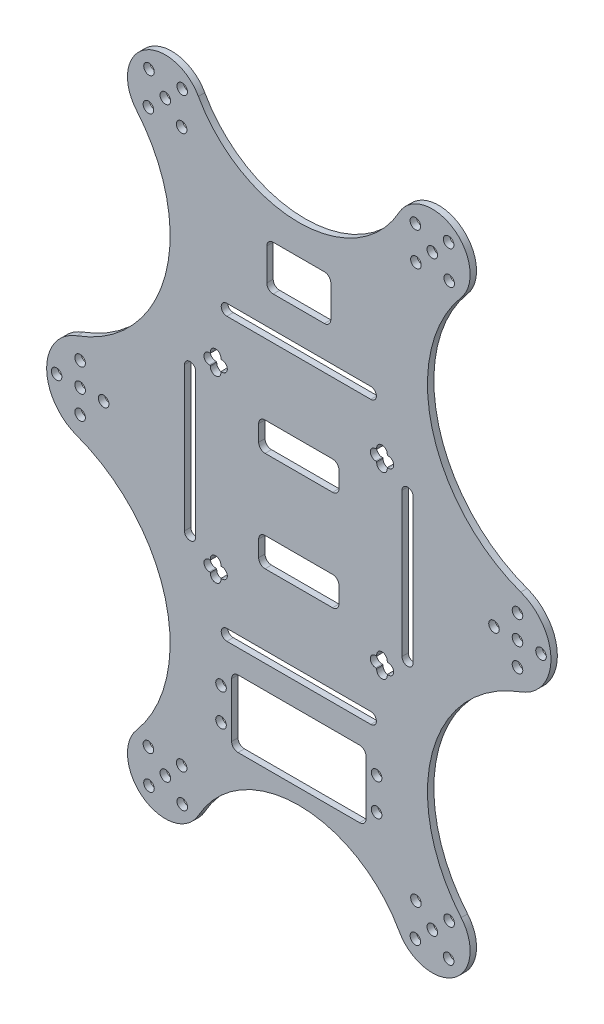
SolidWorks part; units mm, degrees
ref_plane "前视基准面" through (0, 0, 0) normal (0, 0, 1) x (1, 0, 0)
ref_plane "上视基准面" through (0, 0, 0) normal (0, 1, 0) x (1, 0, 0)
ref_plane "右视基准面" through (0, 0, 0) normal (1, 0, 0) x (0, 0, -1)
sketch "草图1" plane through (0, 0, 0) normal (0, 0, 1) x (1, 0, 0)
  line L0 (4.4926, -1.2596) -> (4.4926, -27.7633) construction
  line L1 (109.289, 84.436) -> (119.8633, 74.2245) construction
  line L2 (-7.014, -12.3723) -> (212.2703, -12.3723) construction
  line L3 (26.0221, 84.6174) -> (36.2336, 74.0431) construction
  line L4 (36.415, 84.436) -> (25.8407, 74.2245) construction
  line L5 (72.852, 157.0661) -> (72.852, -150.5607) construction
  line L6 (119.6818, 84.6174) -> (109.4704, 74.0431) construction
  line L7 (141.2114, -1.2596) -> (141.2114, -27.7633) construction
  line L8 (119.6818, -109.362) -> (109.4704, -98.7877) construction
  line L9 (36.415, -109.1806) -> (25.8407, -98.9691) construction
  line L10 (26.0221, -109.362) -> (36.2336, -98.7877) construction
  line L11 (109.289, -109.1806) -> (119.8633, -98.9691) construction
  line L12 (95.352, 33.3777) -> (50.352, 33.3777)
  line L13 (38.852, 21.4961) -> (38.852, -51.8522) construction
  line L14 (40.602, 10.1277) -> (40.602, -34.8723)
  line L15 (37.102, -34.8723) -> (37.102, 10.1277)
  line L16 (108.602, -34.8723) -> (108.602, 10.1277)
  line L17 (105.102, 10.1277) -> (105.102, -34.8723)
  line L18 (95.352, -58.1223) -> (50.352, -58.1223)
  line L19 (50.352, 29.8777) -> (95.352, 29.8777)
  line L20 (50.352, -54.6223) -> (95.352, -54.6223)
  line L21 (106.165, 15.6277) -> (41.102, 15.6277) construction
  line L22 (92.7157, 50.1512) -> (51.4618, 50.1512) construction
  line L23 (98.852, 21.4961) -> (98.852, -45.901) construction
  line L24 (80.852, 57.1512) -> (64.852, 57.1512)
  line L25 (82.852, 55.1512) -> (82.852, 45.1512)
  line L26 (80.852, 43.1512) -> (64.852, 43.1512)
  line L27 (62.852, 55.1512) -> (62.852, 45.1512)
  line L28 (82.852, 57.1512) -> (62.852, 43.1512) construction
  line L29 (82.852, 43.1512) -> (62.852, 57.1512) construction
  line L30 (96.852, 13.9777) -> (97.202, 13.9777)
  line L31 (96.852, 17.2777) -> (97.202, 17.2777)
  line L32 (100.502, 17.6277) -> (100.502, 17.2777)
  line L33 (100.852, 13.9777) -> (100.502, 13.9777)
  line L34 (97.202, 13.6277) -> (97.202, 13.9777)
  line L35 (100.502, 13.9777) -> (100.502, 13.6277)
  line L36 (100.502, 17.2777) -> (100.852, 17.2777)
  line L37 (97.202, 17.2777) -> (97.202, 17.6277)
  line L38 (97.202, 13.9777) -> (96.852, 13.9777)
  line L39 (100.502, 13.9777) -> (100.852, 13.9777)
  line L40 (48.852, 13.9777) -> (48.502, 13.9777)
  line L41 (48.502, 13.6277) -> (48.502, 13.9777)
  line L42 (45.202, 13.9777) -> (45.202, 13.6277)
  line L43 (44.852, 13.9777) -> (45.202, 13.9777)
  line L44 (45.202, 17.2777) -> (44.852, 17.2777)
  line L45 (48.852, 17.2777) -> (48.502, 17.2777)
  line L46 (48.502, 17.2777) -> (48.502, 17.6277)
  line L47 (45.202, 17.6277) -> (45.202, 17.2777)
  line L48 (97.202, -38.3723) -> (97.202, -38.7223)
  line L49 (96.852, -38.7223) -> (97.202, -38.7223)
  line L50 (100.502, -38.7223) -> (100.502, -38.3723)
  line L51 (100.852, -38.7223) -> (100.502, -38.7223)
  line L52 (100.502, -42.0223) -> (100.852, -42.0223)
  line L53 (100.502, -42.3723) -> (100.502, -42.0223)
  line L54 (97.202, -42.0223) -> (97.202, -42.3723)
  line L55 (96.852, -42.0223) -> (97.202, -42.0223)
  line L56 (48.852, -42.0223) -> (48.502, -42.0223)
  line L57 (48.502, -42.0223) -> (48.502, -42.3723)
  line L58 (45.202, -42.3723) -> (45.202, -42.0223)
  line L59 (45.202, -42.0223) -> (44.852, -42.0223)
  line L60 (44.852, -38.7223) -> (45.202, -38.7223)
  line L61 (45.202, -38.7223) -> (45.202, -38.3723)
  line L62 (48.852, -38.7223) -> (48.502, -38.7223)
  line L63 (48.502, -38.3723) -> (48.502, -38.7223)
  line L64 (46.852, 23.6168) -> (46.852, -45.901) construction
  line L65 (40.602, -40.3723) -> (105.102, -40.3723) construction
  line L66 (62.3026, -23.485) -> (83.4013, -23.485)
  line L67 (62.3026, 7.765) -> (83.4013, 7.765)
  line L68 (53.852, -65.478) -> (91.852, -65.478)
  line L69 (51.852, -67.478) -> (51.852, -84.478)
  line L70 (53.852, -86.478) -> (91.852, -86.478)
  line L71 (93.852, -67.478) -> (93.852, -84.478)
  line L72 (51.852, -65.478) -> (93.852, -86.478) construction
  line L73 (51.852, -86.478) -> (93.852, -65.478) construction
  line L74 (60.3026, 5.765) -> (60.3026, 0.7404)
  line L75 (62.3026, -1.2596) -> (83.4013, -1.2596)
  line L76 (85.4013, 5.765) -> (85.4013, 0.7404)
  line L77 (60.3026, 7.765) -> (85.4013, -1.2596) construction
  line L78 (60.3026, -1.2596) -> (85.4013, 7.765) construction
  line L79 (85.4013, -30.5096) -> (85.4013, -25.485)
  line L80 (62.3026, -32.5096) -> (83.4013, -32.5096)
  line L81 (60.3026, -30.5096) -> (60.3026, -25.485)
  line L82 (60.3026, -23.485) -> (85.4013, -32.5096) construction
  line L83 (60.3026, -32.5096) -> (85.4013, -23.485) construction
  circle A0 centre (11.8426, -12.3723) radius 1.65
  arc A1 (3.4788, 1.1401) -> (22.098, 71.5511) centre (-11.7565, 42.8361) ccw
  arc A2 (22.0964, 71.553) -> (41.4673, 84.9489) centre (31.1278, 79.1967) cw
  arc A3 (41.4673, 84.9489) -> (104.2366, 84.9489) centre (72.852, 102.4092) ccw
  arc A4 (22.098, 71.5511) -> (22.0964, 71.553) centre (23.8782, 73.061) cw
  circle A5 centre (119.6818, 84.6174) radius 1.65
  circle A6 centre (36.415, 84.436) radius 1.65
  circle A7 centre (36.2336, 74.0431) radius 1.65
  circle A8 centre (4.4926, -19.7223) radius 1.65
  circle A9 centre (114.5761, 79.3303) radius 1.65
  circle A10 centre (119.8633, 74.2245) radius 1.65
  circle A11 centre (141.2114, -5.0223) radius 1.65
  circle A12 centre (109.4704, 74.0431) radius 1.65
  circle A13 centre (148.5614, -12.3723) radius 1.65
  circle A14 centre (141.2114, -19.7223) radius 1.65
  circle A15 centre (141.2114, -12.3723) radius 1.65
  circle A16 centre (109.289, 84.436) radius 1.65
  circle A17 centre (133.8614, -12.3723) radius 1.65
  circle A18 centre (141.2114, -5.0223) radius 1.65
  arc A19 (142.2251, -25.8847) -> (142.2251, 1.1401) centre (137.2878, -12.3723) ccw
  arc A20 (123.6059, 71.5511) -> (123.6075, 71.553) centre (121.8257, 73.061) ccw
  arc A21 (123.6075, 71.553) -> (104.2366, 84.9489) centre (114.5761, 79.1967) ccw
  arc A22 (142.2251, 1.1401) -> (123.6059, 71.5511) centre (157.4605, 42.8361) cw
  circle A23 centre (4.4926, -5.0223) radius 1.65
  circle A24 centre (26.0221, -109.362) radius 1.65
  circle A25 centre (31.1278, -104.0749) radius 1.65
  circle A26 centre (25.8407, -98.9691) radius 1.65
  circle A27 centre (25.8407, 74.2245) radius 1.65
  circle A28 centre (31.1278, 79.3303) radius 1.65
  circle A29 centre (26.0221, 84.6174) radius 1.65
  arc A30 (142.2251, -25.8847) -> (123.6059, -96.2957) centre (157.4605, -67.5808) ccw
  arc A31 (123.6075, -96.2976) -> (104.2366, -109.6935) centre (114.5761, -103.9413) cw
  arc A32 (123.6059, -96.2957) -> (123.6075, -96.2976) centre (121.8257, -97.8056) cw
  circle A33 centre (109.289, -109.1806) radius 1.65
  circle A34 centre (109.4704, -98.7877) radius 1.65
  circle A35 centre (119.8633, -98.9691) radius 1.65
  circle A36 centre (114.5761, -104.0749) radius 1.65
  circle A37 centre (36.2336, -98.7877) radius 1.65
  circle A38 centre (36.415, -109.1806) radius 1.65
  circle A39 centre (119.6818, -109.362) radius 1.65
  arc A40 (22.098, -96.2957) -> (22.0964, -96.2976) centre (23.8782, -97.8056) ccw
  arc A41 (41.4673, -109.6935) -> (104.2366, -109.6935) centre (72.852, -127.1538) cw
  arc A42 (22.0964, -96.2976) -> (41.4673, -109.6935) centre (31.1278, -103.9413) ccw
  arc A43 (3.4788, -25.8847) -> (22.098, -96.2957) centre (-11.7565, -67.5808) cw
  arc A44 (105.102, -34.8723) -> (108.602, -34.8723) centre (106.852, -34.8723) ccw
  arc A45 (105.102, 10.1277) -> (108.602, 10.1277) centre (106.852, 10.1277) cw
  arc A46 (95.352, 29.8777) -> (95.352, 33.3777) centre (95.352, 31.6277) ccw
  arc A47 (50.352, 29.8777) -> (50.352, 33.3777) centre (50.352, 31.6277) cw
  arc A48 (40.602, 10.1277) -> (37.102, 10.1277) centre (38.852, 10.1277) ccw
  arc A49 (40.602, -34.8723) -> (37.102, -34.8723) centre (38.852, -34.8723) cw
  arc A50 (95.352, -54.6223) -> (95.352, -58.1223) centre (95.352, -56.3723) cw
  arc A51 (50.352, -54.6223) -> (50.352, -58.1223) centre (50.352, -56.3723) ccw
  arc A52 (96.852, 13.9777) -> (96.852, 17.2777) centre (96.852, 15.6277) cw
  arc A53 (96.852, -38.7223) -> (96.852, -42.0223) centre (96.852, -40.3723) ccw
  arc A54 (97.202, -38.3723) -> (100.502, -38.3723) centre (98.852, -38.3723) cw
  arc A55 (100.852, -38.7223) -> (100.852, -42.0223) centre (100.852, -40.3723) cw
  arc A56 (100.852, 13.9777) -> (100.852, 17.2777) centre (100.852, 15.6277) ccw
  arc A57 (97.202, 13.6277) -> (100.502, 13.6277) centre (98.852, 13.6277) ccw
  arc A58 (96.852, 17.2777) -> (96.852, 13.9777) centre (96.852, 15.6277) ccw
  arc A59 (100.502, 17.6277) -> (97.202, 17.6277) centre (98.852, 17.6277) ccw
  arc A60 (48.502, 13.6277) -> (45.202, 13.6277) centre (46.852, 13.6277) cw
  arc A61 (48.852, 13.9777) -> (48.852, 17.2777) centre (48.852, 15.6277) ccw
  arc A62 (44.852, 13.9777) -> (44.852, 17.2777) centre (44.852, 15.6277) cw
  arc A63 (45.202, 17.6277) -> (48.502, 17.6277) centre (46.852, 17.6277) cw
  arc A64 (100.502, -42.3723) -> (97.202, -42.3723) centre (98.852, -42.3723) cw
  arc A65 (45.202, -42.3723) -> (48.502, -42.3723) centre (46.852, -42.3723) ccw
  arc A66 (44.852, -38.7223) -> (44.852, -42.0223) centre (44.852, -40.3723) ccw
  arc A67 (48.502, -38.3723) -> (45.202, -38.3723) centre (46.852, -38.3723) ccw
  arc A68 (48.852, -38.7223) -> (48.852, -42.0223) centre (48.852, -40.3723) cw
  arc A69 (64.852, 43.1512) -> (62.852, 45.1512) centre (64.852, 45.1512) cw
  arc A70 (62.852, 55.1512) -> (64.852, 57.1512) centre (64.852, 55.1512) cw
  arc A71 (80.852, 57.1512) -> (82.852, 55.1512) centre (80.852, 55.1512) cw
  arc A72 (80.852, 43.1512) -> (82.852, 45.1512) centre (80.852, 45.1512) ccw
  circle A73 centre (48.537, -70.978) radius 1.65
  circle A74 centre (48.537, -80.978) radius 1.65
  circle A75 centre (97.167, -80.978) radius 1.65
  circle A76 centre (97.167, -70.978) radius 1.65
  arc A77 (51.852, -67.478) -> (53.852, -65.478) centre (53.852, -67.478) cw
  arc A78 (93.852, -67.478) -> (91.852, -65.478) centre (91.852, -67.478) ccw
  arc A79 (51.852, -84.478) -> (53.852, -86.478) centre (53.852, -84.478) ccw
  circle A80 centre (-2.8574, -12.3723) radius 1.65
  circle A81 centre (4.4926, -12.3723) radius 1.65
  arc A82 (91.852, -86.478) -> (93.852, -84.478) centre (91.852, -84.478) ccw
  arc A83 (60.3026, 5.765) -> (62.3026, 7.765) centre (62.3026, 5.765) cw
  arc A84 (60.3026, 0.7404) -> (62.3026, -1.2596) centre (62.3026, 0.7404) ccw
  arc A85 (85.4013, 5.765) -> (83.4013, 7.765) centre (83.4013, 5.765) ccw
  arc A86 (85.4013, 0.7404) -> (83.4013, -1.2596) centre (83.4013, 0.7404) cw
  arc A87 (60.3026, -30.5096) -> (62.3026, -32.5096) centre (62.3026, -30.5096) ccw
  arc A88 (85.4013, -25.485) -> (83.4013, -23.485) centre (83.4013, -25.485) ccw
  arc A89 (60.3026, -25.485) -> (62.3026, -23.485) centre (62.3026, -25.485) cw
  arc A90 (85.4013, -30.5096) -> (83.4013, -32.5096) centre (83.4013, -30.5096) cw
  arc A104 (3.4788, -25.8847) -> (3.4788, 1.1401) centre (8.4161, -12.3723) cw
  point P129 (72.852, 50.1512)
  point P149 (98.852, 15.6277)
  point P168 (98.852, 15.6277)
  point P228 (72.852, -75.978)
  point P233 (72.852, -75.978)
  point P252 (72.852, 3.2527)
  point P261 (72.852, -27.9973)
  dimension "D1" = 14.7
  dimension "D2" = 14.7
  dimension "D3" = 14.7
  dimension "D4" = 14.7
  dimension "D5" = 3.5
  dimension "D6" = 34
  dimension "D8" = 151.4188
  dimension "D9" = 22.5
  dimension "D7" = 4
  dimension "D10" = 3.5
  dimension "D13" = 2
  dimension "D14" = 2
  dimension "D15" = 2
  dimension "D16" = 2
  dimension "D20" = 3.3
  dimension "D19" = 2
  dimension "D22" = 2
  dimension "D23" = 2
  dimension "D24" = 2
  dimension "D25" = 2
  dimension "D26" = 2
  dimension "D27" = 2
  dimension "D28" = 2
  dimension "D29" = 2
  dimension "D30" = 2
  dimension "D31" = 2
  dimension "D32" = 2
  dimension "D11" = 20
  dimension "D12" = 14
  dimension "D17" = 21
  dimension "D18" = 42
  dimension "D21" = 10
extrude "凸台-拉伸1" add sketch "草图1" along normal blind 2
